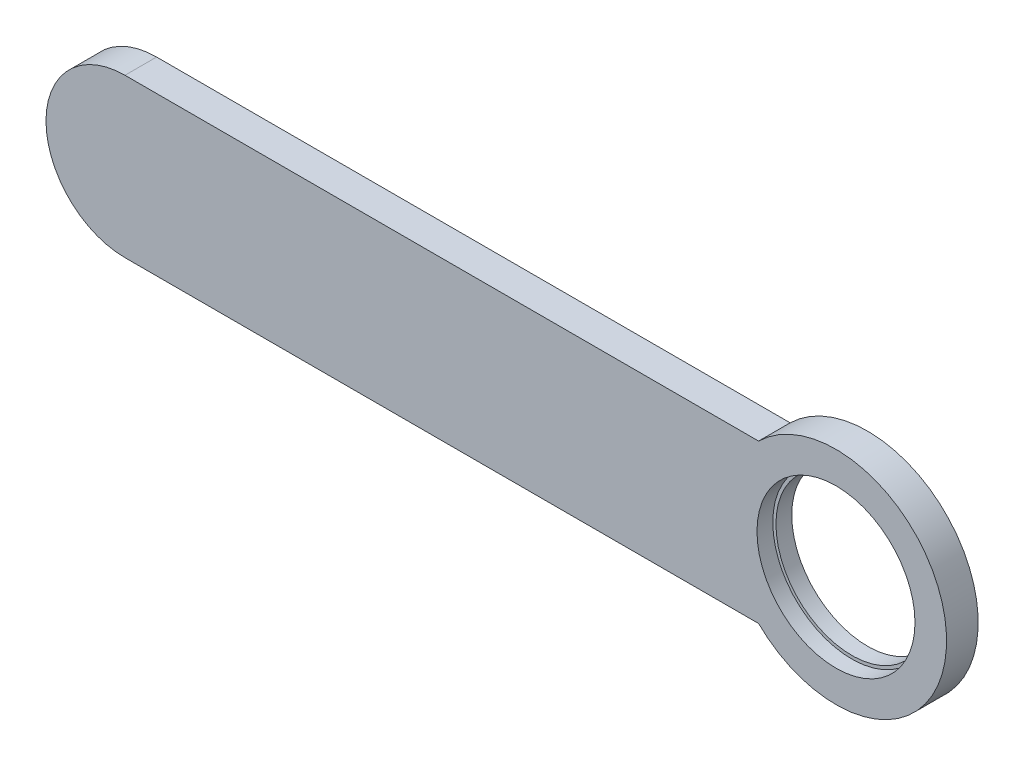
SolidWorks part; units mm, degrees
material "PVC rigide"
ref_plane "Plan de face" through (0, 0, 0) normal (0, 0, 1) x (1, 0, 0)
ref_plane "Plan de dessus" through (0, 0, 0) normal (0, 1, 0) x (1, 0, 0)
ref_plane "Plan de droite" through (0, 0, 0) normal (1, 0, 0) x (0, 0, -1)
sketch "Esquisse1" plane through (0, 0, 0) normal (0, 0, 1) x (1, 0, 0)
  line L0 (0, 0) -> (-450, 0) construction
  line L1 (0, -70) -> (-450, -70)
  line L2 (0, 70) -> (-450, 70)
  circle A0 centre (0, 0) radius 50
  arc A1 (0, -70) -> (0, 70) centre (0, 0) ccw
  arc A2 (-450, 70) -> (-450, -70) centre (-450, 0) ccw
  point P4 (-225, 0)
  dimension "D1" = 100
  dimension "D3" = 20
  dimension "D2" = 450
extrude "Boss.-Extru.1" add sketch "Esquisse1" along normal blind 20
sketch "Esquisse2" plane through (0, 0, 0) normal (0, 0, -1) x (-1, 0, 0)
  circle A2 centre (0, 0) radius 48
  circle A3 centre (0, 0) radius 50 construction
  circle A4 centre (0, 0) radius 50
  dimension "D1" = 2
extrude "Boss.-Extru.2" add sketch "Esquisse2" against normal blind 10
sketch "Esquisse3" plane through (0, 0, 0) normal (0, 0, -1) x (-1, 0, 0)
  line L0 (450, -50) -> (48.9898, -50)
  line L1 (450, 50) -> (48.9898, 50)
  arc A0 (450, -50) -> (450, 50) centre (450, 0) ccw
  arc A1 (48.9898, 50) -> (48.9898, -50) centre (0, 0) ccw
  dimension "D1" = 100
extrude "Enlèv. mat.-Extru.1" cut sketch "Esquisse3" against normal through all flip side to cut
